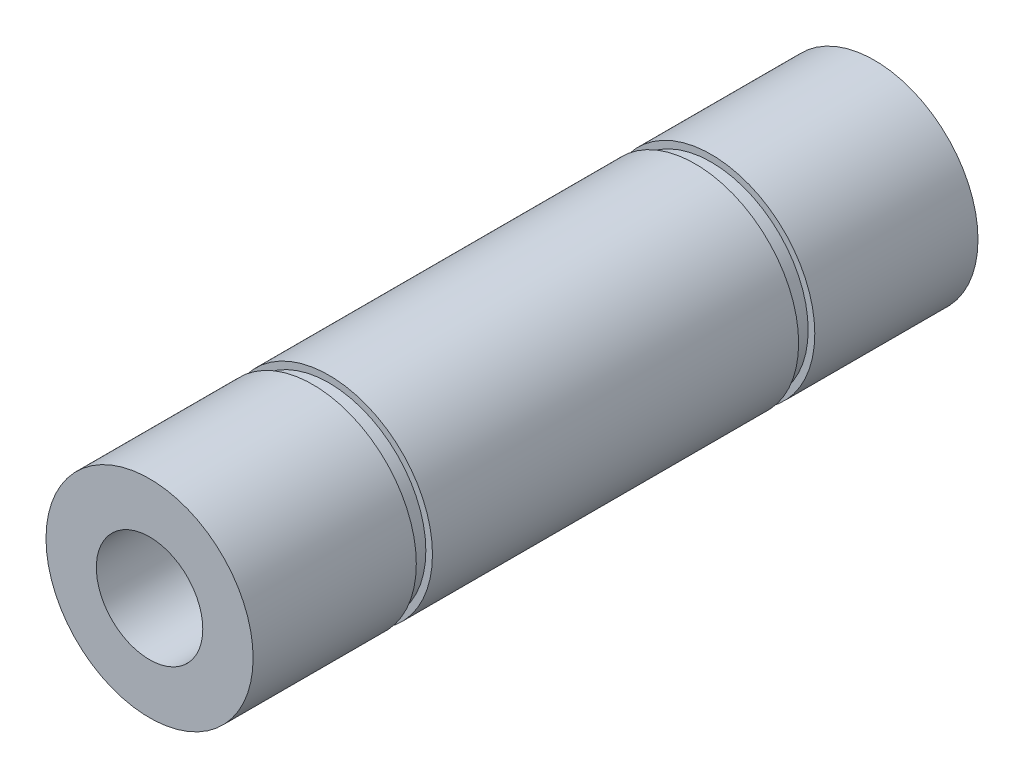
SolidWorks part; units mm, degrees
material "SS 304 (Default)"
ref_plane "Front Plane" through (0, 0, 0) normal (0, 0, 1) x (1, 0, 0)
ref_plane "Top Plane" through (0, 0, 0) normal (0, 1, 0) x (1, 0, 0)
ref_plane "Right Plane" through (0, 0, 0) normal (1, 0, 0) x (0, 0, -1)
sketch "Sketch1" plane through (0, 0, 0) normal (0, 0, 1) x (1, 0, 0)
  circle A0 centre (0, 0) radius 6.35
  dimension "Diameter" = 12.7
extrude "Extrude1" add sketch "Sketch1" along normal mid plane 44.45
hole_wizard "5/16-18 Tapped Hole1" positions "Sketch2" profile "Sketch3" tap size "5/16-18" standard "ANSI Inch"
sketch "Sketch2" plane through (0, 0, 22.225) normal (0, 0, 1) x (1, 0, 0)
  point P0 (0, 0)
sketch "Sketch3" plane through (0, 0, 22.225) normal (1, 0, 0) x (0, -1, 0)
  line L0 (0, 0) -> (0, 22.2811)
  line L1 (0, 22.2811) -> (3.2639, 20.32)
  line L2 (3.2639, 20.32) -> (3.2639, 0)
  line L5 (3.2639, 0) -> (0, 0)
  line L10 (0, 22.2811) -> (-3.2639, 20.32) construction
  line L11 (0, -6.35) -> (0, 107.95) construction
  dimension "Tap Drill Dia." = 6.5278
  dimension "Tap Drill Depth" = 20.32
  dimension "Drill Angle" = 118
cosmetic thread "Hole Thread1" parameters "D1"=16.002, "D2"=7.9375
hole_wizard "5/16-18 Tapped Hole2" positions "Sketch4" profile "Sketch5" tap size "5/16-18" standard "ANSI Inch"
sketch "Sketch4" plane through (0, 0, -22.225) normal (0, 0, -1) x (-1, 0, 0)
  point P0 (0, 0)
sketch "Sketch5" plane through (0, 0, -22.225) normal (1, 0, 0) x (0, 1, 0)
  line L0 (0, 0) -> (0, 22.2811)
  line L1 (0, 22.2811) -> (3.2639, 20.32)
  line L2 (3.2639, 20.32) -> (3.2639, 0)
  line L5 (3.2639, 0) -> (0, 0)
  line L10 (0, 22.2811) -> (-3.2639, 20.32) construction
  line L11 (0, -6.35) -> (0, 107.95) construction
  dimension "Tap Drill Dia." = 6.5278
  dimension "Tap Drill Depth" = 20.32
  dimension "Drill Angle" = 118
cosmetic thread "Hole Thread2" parameters "D1"=16.002, "D2"=7.9375
sketch "Sketch6" plane through (0, 0, 0) normal (1, 0, 0) x (0, 0, -1)
  line L0 (22.225, 6.35) -> (-22.225, 6.35) construction
  line L1 (11.2268, 6.35) -> (12.2174, 6.35)
  line L2 (11.2268, 6.35) -> (11.2268, 5.9436)
  line L3 (11.2268, 5.9436) -> (12.2174, 5.9436)
  line L4 (12.2174, 6.35) -> (12.2174, 5.9436)
  dimension "D1" = 11.2268
  dimension "D2" = 0.9906
  dimension "D3" = 5.9436
revolve "Cut-Revolve1" cut sketch "Sketch6" angle 360 about axis through (0, 0, 22.225) along (0, 0, -1)
mirror "Mirror1" about plane through (0, 0, 0) normal (0, 0, 1) of "Cut-Revolve1"
